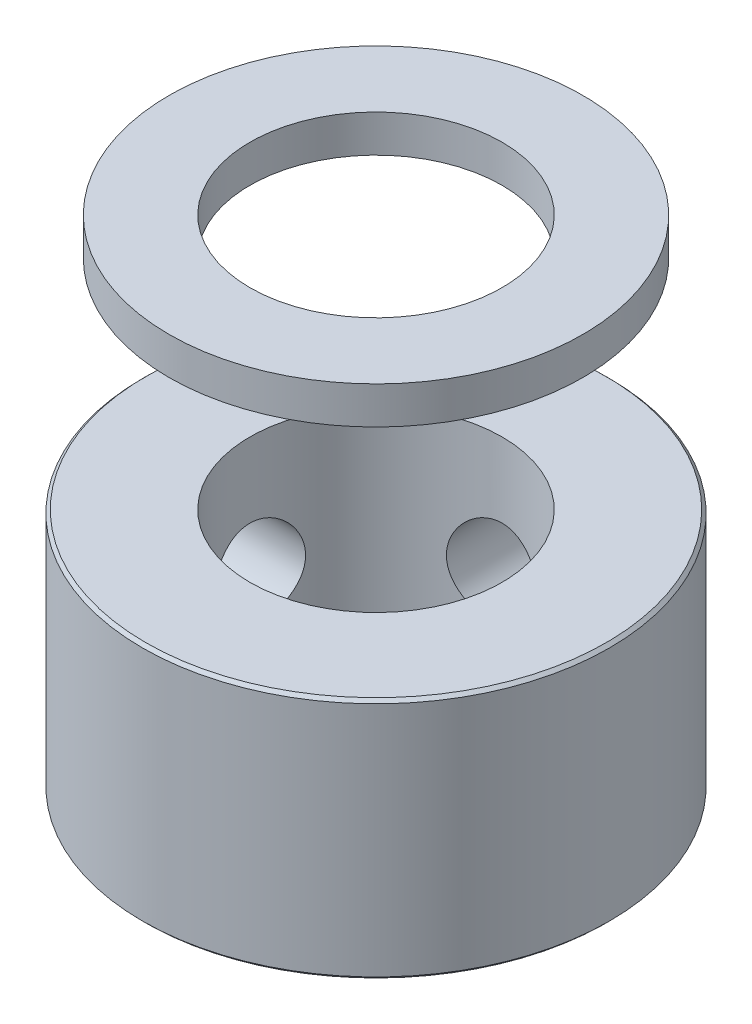
SolidWorks part; units mm, degrees
material "6061 slitina"
ref_plane "Přední rovina" through (0, 0, 0) normal (0, 0, 1) x (1, 0, 0)
ref_plane "Horní rovina" through (0, 0, 0) normal (0, 1, 0) x (1, 0, 0)
ref_plane "Pravá rovina" through (0, 0, 0) normal (1, 0, 0) x (0, 0, -1)
sketch "Skica1" plane through (0, 0, 0) normal (0, 1, 0) x (1, 0, 0)
  circle A0 centre (0, 0) radius 2.5
  arc B0 (-5.7301, 1.0983) -> (-5.3872, 2.2403) centre (-5.6803, 1.7058) ccw
  arc B1 (-5.7301, 1.0983) -> (-5.922, 1.0859) centre (-5.7841, 0.4401) ccw
  arc B2 (-5.922, 1.0859) -> (-6.0197, 1.0387) centre (-5.8743, 0.8624) ccw
  arc B3 (-6.0197, 1.0387) -> (-6.0791, 0.6004) centre (0, 0) ccw
  arc B4 (-6.0791, 0.6004) -> (-5.9974, 0.5289) centre (-5.892, 0.7317) ccw
  arc B5 (-5.9974, 0.5289) -> (-5.8158, 0.466) centre (-5.6927, 1.1148) ccw
  arc B6 (-5.7891, -0.7262) -> (-5.8158, 0.466) centre (-5.9294, -0.133) ccw
  arc B7 (-5.7891, -0.7262) -> (-5.9677, -0.7972) centre (-5.637, -1.3689) ccw
  arc B8 (-5.9677, -0.7972) -> (-6.0461, -0.8723) centre (-5.8532, -0.9951) ccw
  arc B9 (-6.0461, -0.8723) -> (-5.9671, -1.3075) centre (0, 0) ccw
  arc B10 (-5.9671, -1.3075) -> (-5.8673, -1.3503) centre (-5.8297, -1.1248) ccw
  arc B11 (-5.8673, -1.3503) -> (-5.6751, -1.354) centre (-5.7586, -0.6989) ccw
  arc B12 (-5.2813, -2.4796) -> (-5.6751, -1.354) centre (-5.5981, -1.9587) ccw
  arc B13 (-5.2813, -2.4796) -> (-5.4293, -2.6023) centre (-4.9381, -3.0438) ccw
  arc B14 (-5.4293, -2.6023) -> (-5.4806, -2.698) centre (-5.2593, -2.7551) ccw
  arc B15 (-5.4806, -2.698) -> (-5.271, -3.0875) centre (0, 0) ccw
  arc B16 (-5.271, -3.0875) -> (-5.1629, -3.0973) centre (-5.1968, -2.8713) ccw
  arc B17 (-5.1629, -3.0973) -> (-4.979, -3.0415) centre (-5.2608, -2.4442) ccw
  arc B18 (-4.2566, -3.9902) -> (-4.979, -3.0415) centre (-4.7188, -3.5928) ccw
  arc B19 (-4.2566, -3.9902) -> (-4.3594, -4.1527) centre (-3.7559, -4.4208) ccw
  arc B20 (-4.3594, -4.1527) -> (-4.3786, -4.2595) centre (-4.1505, -4.2455) ccw
  arc B21 (-4.3786, -4.2595) -> (-4.059, -4.5652) centre (0, 0) ccw
  arc B22 (-4.059, -4.5652) -> (-3.9531, -4.5412) centre (-4.0552, -4.3366) ccw
  arc B23 (-3.9531, -4.5412) -> (-3.7954, -4.4312) centre (-4.248, -3.9503) ccw
  arc B24 (-2.8152, -5.1103) -> (-3.7954, -4.4312) centre (-3.3776, -4.8751) ccw
  arc B25 (-2.8152, -5.1103) -> (-2.8628, -5.2965) centre (-2.2059, -5.3651) ccw
  arc B26 (-2.8628, -5.2965) -> (-2.8481, -5.4041) centre (-2.6354, -5.3203) ccw
  arc B27 (-2.8481, -5.4041) -> (-2.4496, -5.596) centre (0, 0) ccw
  arc B28 (-2.4496, -5.596) -> (-2.3563, -5.5405) centre (-2.5166, -5.3775) ccw
  arc B29 (-2.3563, -5.5405) -> (-2.2403, -5.3872) centre (-2.8194, -5.0696) ccw
  arc B30 (-1.0983, -5.7301) -> (-2.2403, -5.3872) centre (-1.7058, -5.6803) ccw
  arc B31 (-1.0983, -5.7301) -> (-1.0859, -5.922) centre (-0.4401, -5.7841) ccw
  arc B32 (-1.0859, -5.922) -> (-1.0387, -6.0197) centre (-0.8624, -5.8743) ccw
  arc B33 (-1.0387, -6.0197) -> (-0.6004, -6.0791) centre (0, 0) ccw
  arc B34 (-0.6004, -6.0791) -> (-0.5289, -5.9974) centre (-0.7317, -5.892) ccw
  arc B35 (-0.5289, -5.9974) -> (-0.466, -5.8158) centre (-1.1148, -5.6927) ccw
  arc B36 (0.7262, -5.7891) -> (-0.466, -5.8158) centre (0.133, -5.9294) ccw
  arc B37 (0.7262, -5.7891) -> (0.7972, -5.9677) centre (1.3689, -5.637) ccw
  arc B38 (0.7972, -5.9677) -> (0.8723, -6.0461) centre (0.9951, -5.8532) ccw
  arc B39 (0.8723, -6.0461) -> (1.3075, -5.9671) centre (0, 0) ccw
  arc B40 (1.3075, -5.9671) -> (1.3503, -5.8673) centre (1.1248, -5.8297) ccw
  arc B41 (1.3503, -5.8673) -> (1.354, -5.6751) centre (0.6989, -5.7586) ccw
  arc B42 (2.4796, -5.2813) -> (1.354, -5.6751) centre (1.9587, -5.5981) ccw
  arc B43 (2.4796, -5.2813) -> (2.6023, -5.4293) centre (3.0438, -4.9381) ccw
  arc B44 (2.6023, -5.4293) -> (2.698, -5.4806) centre (2.7551, -5.2593) ccw
  arc B45 (2.698, -5.4806) -> (3.0875, -5.271) centre (0, 0) ccw
  arc B46 (3.0875, -5.271) -> (3.0973, -5.1629) centre (2.8713, -5.1968) ccw
  arc B47 (3.0973, -5.1629) -> (3.0415, -4.979) centre (2.4442, -5.2608) ccw
  arc B48 (3.9902, -4.2566) -> (3.0415, -4.979) centre (3.5928, -4.7188) ccw
  arc B49 (3.9902, -4.2566) -> (4.1527, -4.3594) centre (4.4208, -3.7559) ccw
  arc B50 (4.1527, -4.3594) -> (4.2595, -4.3786) centre (4.2455, -4.1505) ccw
  arc B51 (4.2595, -4.3786) -> (4.5652, -4.059) centre (0, 0) ccw
  arc B52 (4.5652, -4.059) -> (4.5412, -3.9531) centre (4.3366, -4.0552) ccw
  arc B53 (4.5412, -3.9531) -> (4.4312, -3.7954) centre (3.9503, -4.248) ccw
  arc B54 (5.1103, -2.8152) -> (4.4312, -3.7954) centre (4.8751, -3.3776) ccw
  arc B55 (5.1103, -2.8152) -> (5.2965, -2.8628) centre (5.3651, -2.2059) ccw
  arc B56 (5.2965, -2.8628) -> (5.4041, -2.8481) centre (5.3203, -2.6354) ccw
  arc B57 (5.4041, -2.8481) -> (5.596, -2.4496) centre (0, 0) ccw
  arc B58 (5.596, -2.4496) -> (5.5405, -2.3563) centre (5.3775, -2.5166) ccw
  arc B59 (5.5405, -2.3563) -> (5.3872, -2.2403) centre (5.0696, -2.8194) ccw
  arc B60 (5.7301, -1.0983) -> (5.3872, -2.2403) centre (5.6803, -1.7058) ccw
  arc B61 (5.7301, -1.0983) -> (5.922, -1.0859) centre (5.7841, -0.4401) ccw
  arc B62 (5.922, -1.0859) -> (6.0197, -1.0387) centre (5.8743, -0.8624) ccw
  arc B63 (6.0197, -1.0387) -> (6.0791, -0.6004) centre (0, 0) ccw
  arc B64 (6.0791, -0.6004) -> (5.9974, -0.5289) centre (5.892, -0.7317) ccw
  arc B65 (5.9974, -0.5289) -> (5.8158, -0.466) centre (5.6927, -1.1148) ccw
  arc B66 (5.7891, 0.7262) -> (5.8158, -0.466) centre (5.9294, 0.133) ccw
  arc B67 (5.7891, 0.7262) -> (5.9677, 0.7972) centre (5.637, 1.3689) ccw
  arc B68 (5.9677, 0.7972) -> (6.0461, 0.8723) centre (5.8532, 0.9951) ccw
  arc B69 (6.0461, 0.8723) -> (5.9671, 1.3075) centre (0, 0) ccw
  arc B70 (5.9671, 1.3075) -> (5.8673, 1.3503) centre (5.8297, 1.1248) ccw
  arc B71 (5.8673, 1.3503) -> (5.6751, 1.354) centre (5.7586, 0.6989) ccw
  arc B72 (5.2813, 2.4796) -> (5.6751, 1.354) centre (5.5981, 1.9587) ccw
  arc B73 (5.2813, 2.4796) -> (5.4293, 2.6023) centre (4.9381, 3.0438) ccw
  arc B74 (5.4293, 2.6023) -> (5.4806, 2.698) centre (5.2593, 2.7551) ccw
  arc B75 (5.4806, 2.698) -> (5.271, 3.0875) centre (0, 0) ccw
  arc B76 (5.271, 3.0875) -> (5.1629, 3.0973) centre (5.1968, 2.8713) ccw
  arc B77 (5.1629, 3.0973) -> (4.979, 3.0415) centre (5.2608, 2.4442) ccw
  arc B78 (4.2566, 3.9902) -> (4.979, 3.0415) centre (4.7188, 3.5928) ccw
  arc B79 (4.2566, 3.9902) -> (4.3594, 4.1527) centre (3.7559, 4.4208) ccw
  arc B80 (4.3594, 4.1527) -> (4.3786, 4.2595) centre (4.1505, 4.2455) ccw
  arc B81 (4.3786, 4.2595) -> (4.059, 4.5652) centre (0, 0) ccw
  arc B82 (4.059, 4.5652) -> (3.9531, 4.5412) centre (4.0552, 4.3366) ccw
  arc B83 (3.9531, 4.5412) -> (3.7954, 4.4312) centre (4.248, 3.9503) ccw
  arc B84 (2.8152, 5.1103) -> (3.7954, 4.4312) centre (3.3776, 4.8751) ccw
  arc B85 (2.8152, 5.1103) -> (2.8628, 5.2965) centre (2.2059, 5.3651) ccw
  arc B86 (2.8628, 5.2965) -> (2.8481, 5.4041) centre (2.6354, 5.3203) ccw
  arc B87 (2.8481, 5.4041) -> (2.4496, 5.596) centre (0, 0) ccw
  arc B88 (2.4496, 5.596) -> (2.3563, 5.5405) centre (2.5166, 5.3775) ccw
  arc B89 (2.3563, 5.5405) -> (2.2403, 5.3872) centre (2.8194, 5.0696) ccw
  arc B90 (1.0983, 5.7301) -> (2.2403, 5.3872) centre (1.7058, 5.6803) ccw
  arc B91 (1.0983, 5.7301) -> (1.0859, 5.922) centre (0.4401, 5.7841) ccw
  arc B92 (1.0859, 5.922) -> (1.0387, 6.0197) centre (0.8624, 5.8743) ccw
  arc B93 (1.0387, 6.0197) -> (0.6004, 6.0791) centre (0, 0) ccw
  arc B94 (0.6004, 6.0791) -> (0.5289, 5.9974) centre (0.7317, 5.892) ccw
  arc B95 (0.5289, 5.9974) -> (0.466, 5.8158) centre (1.1148, 5.6927) ccw
  arc B96 (-0.7262, 5.7891) -> (0.466, 5.8158) centre (-0.133, 5.9294) ccw
  arc B97 (-0.7262, 5.7891) -> (-0.7972, 5.9677) centre (-1.3689, 5.637) ccw
  arc B98 (-0.7972, 5.9677) -> (-0.8723, 6.0461) centre (-0.9951, 5.8532) ccw
  arc B99 (-0.8723, 6.0461) -> (-1.3075, 5.9671) centre (0, 0) ccw
  arc B100 (-1.3075, 5.9671) -> (-1.3503, 5.8673) centre (-1.1248, 5.8297) ccw
  arc B101 (-1.3503, 5.8673) -> (-1.354, 5.6751) centre (-0.6989, 5.7586) ccw
  arc B102 (-2.4796, 5.2813) -> (-1.354, 5.6751) centre (-1.9587, 5.5981) ccw
  arc B103 (-2.4796, 5.2813) -> (-2.6023, 5.4293) centre (-3.0438, 4.9381) ccw
  arc B104 (-2.6023, 5.4293) -> (-2.698, 5.4806) centre (-2.7551, 5.2593) ccw
  arc B105 (-2.698, 5.4806) -> (-3.0875, 5.271) centre (0, 0) ccw
  arc B106 (-3.0875, 5.271) -> (-3.0973, 5.1629) centre (-2.8713, 5.1968) ccw
  arc B107 (-3.0973, 5.1629) -> (-3.0415, 4.979) centre (-2.4442, 5.2608) ccw
  arc B108 (-3.9902, 4.2566) -> (-3.0415, 4.979) centre (-3.5928, 4.7188) ccw
  arc B109 (-3.9902, 4.2566) -> (-4.1527, 4.3594) centre (-4.4208, 3.7559) ccw
  arc B110 (-4.1527, 4.3594) -> (-4.2595, 4.3786) centre (-4.2455, 4.1505) ccw
  arc B111 (-4.2595, 4.3786) -> (-4.5652, 4.059) centre (0, 0) ccw
  arc B112 (-4.5652, 4.059) -> (-4.5412, 3.9531) centre (-4.3366, 4.0552) ccw
  arc B113 (-4.5412, 3.9531) -> (-4.4312, 3.7954) centre (-3.9503, 4.248) ccw
  arc B114 (-5.1103, 2.8152) -> (-4.4312, 3.7954) centre (-4.8751, 3.3776) ccw
  arc B115 (-5.1103, 2.8152) -> (-5.2965, 2.8628) centre (-5.3651, 2.2059) ccw
  arc B116 (-5.2965, 2.8628) -> (-5.4041, 2.8481) centre (-5.3203, 2.6354) ccw
  arc B117 (-5.4041, 2.8481) -> (-5.596, 2.4496) centre (0, 0) ccw
  arc B118 (-5.596, 2.4496) -> (-5.5405, 2.3563) centre (-5.3775, 2.5166) ccw
  arc B119 (-5.5405, 2.3563) -> (-5.3872, 2.2403) centre (-5.0696, 2.8194) ccw
  dimension "D1" = 5
sketch_block_instance "Blok1-1"
sketch_block "Blok1"
extrude "Přidat vysunutím1" add sketch "Skica1" along normal blind 7 from offset 7.8
sketch "Skica2" plane through (0, 7.8, 0) normal (0, -1, 0) x (1, 0, 0)
  circle A0 centre (0, 0) radius 3.5
  circle A1 centre (0, 0) radius 2.5 construction
  circle A2 centre (0, 0) radius 2.5
  dimension "D1" = 7
extrude "Přidat vysunutím2" add sketch "Skica2" along normal blind 7.8
sketch "Skica3" plane through (0, 14.8, 0) normal (0, 1, 0) x (1, 0, 0)
  circle A0 centre (0, 0) radius 3.5
  circle A1 centre (0, 0) radius 2.5 construction
  circle A2 centre (0, 0) radius 2.5
  dimension "D1" = 7
extrude "Přidat vysunutím3" add sketch "Skica3" along normal blind 1.2
sketch "Skica5" plane through (0, 16, 0) normal (0, 1, 0) x (1, 0, 0)
  circle A0 centre (0, 0) radius 7.5
  circle A3 centre (0, 0) radius 3.5 construction
  circle A4 centre (0, 0) radius 3.5
  dimension "D1" = 15
extrude "Přidat vysunutím4" add sketch "Skica5" against normal up to surface (1.2 mm away) separate body up to face at (0, 14.8, 0)
sketch "Skica6" plane through (0, 0, 0) normal (0, -1, 0) x (1, 0, 0)
  circle A0 centre (0, 0) radius 7.5
  circle A1 centre (0, 0) radius 3.5 construction
  circle A2 centre (0, 0) radius 3.5
  circle A3 centre (0, 0) radius 7.5 construction
extrude "Přidat vysunutím5" add sketch "Skica6" against normal up to surface (7.8 mm away) separate body up to face at (0, 7.8, 0)
chamfer "Zkosení1" distance 0.1 angle 45 2 edges at (0, 14.8, 7.5) (0, 16, 7.5)
chamfer "Zkosení2" distance 0.1 angle 45 2 edges at (0, 0, -2.5) (0, 16, 2.5)
chamfer "Zkosení3" distance 0.1 angle 45 2 edges at (0, 0, -7.5) (0, 7.8, 7.5)
sketch "Sketch7" plane through (0, 0, 0) normal (0, -1, 0) x (1, 0, 0)
  circle A1 centre (0, 0) radius 4.05
  dimension "D1" = 8.1
sketch "Sketch8" plane through (0, 16, 0) normal (0, 1, 0) x (1, 0, 0)
  circle A0 centre (0, 0) radius 6.65
extrude "Cut-Extrude2" cut sketch "Sketch8" against normal blind 5 flip side to cut contours A0
ref_plane "Plane1" through (0, 0, -7.5) normal (0, 0, -1) x (-1, 0, 0)
ref_plane "Plane2" through (-7.5, 0, 0) normal (-1, 0, 0) x (0, 0, 1)
sketch "Sketch19" plane through (0, 0, -7.5) normal (0, 0, -1) x (-1, 0, 0)
  line L0 (0, 0.1) -> (0, 7.7)
  line L1 (7.5, 0.1) -> (-7.5, 0.1) construction
  line L2 (7.5, 7.7) -> (-7.5, 7.7) construction
  circle A0 centre (0, 3.9) radius 1.5
extrude "Cut-Extrude6" cut sketch "Sketch19" against normal blind 5 contours A0
sketch "Sketch20" plane through (-7.5, 0, 0) normal (-1, 0, 0) x (0, 0, 1)
  line L0 (0, 0.1) -> (0, 7.7)
  line L1 (-7.5, 0.1) -> (7.5, 0.1) construction
  line L2 (7.5, 7.7) -> (-7.5, 7.7) construction
  circle A0 centre (0, 3.9) radius 1.5
extrude "Cut-Extrude7" cut sketch "Sketch20" against normal blind 5 contours A0
extrude "Cut-Extrude9" cut sketch "Sketch7" against normal blind 20 contours A1
sketch "Sketch23" plane through (0, 0, 0) normal (0, 1, 0) x (1, 0, 0)
  line L1 (0, 7.34) -> (-6.3566, -3.67)
  line L2 (-6.3566, -3.67) -> (6.3566, -3.67)
  line L3 (6.3566, -3.67) -> (0, 7.34)
  circle A0 centre (0, 0) radius 3.67 construction
sketch "Sketch25" plane through (0, 7.8, 0) normal (0, 1, 0) x (1, 0, 0)
  line L0 (-0.7179, 6.0965) -> (-0.9071, 5.7689)
  line L5 (-5.5084, -3.67) -> (-4.5368, -3.67)
  line L6 (5.926, -2.9242) -> (5.4338, -2.0716)
  line L9 (-5.4363, -2.0759) -> (-5.8989, -2.8773)
  line L23 (-3.4987, -3.67) -> (-2.5208, -3.67)
  line L24 (-4.4422, -0.3541) -> (-4.912, -1.1678)
  line L26 (-1.4992, -3.67) -> (-0.513, -3.67)
  line L27 (2.4958, -3.67) -> (3.5189, -3.67)
  line L28 (4.926, -1.192) -> (4.4459, -0.3606)
  line L29 (4.549, -3.67) -> (5.5306, -3.67)
  line L30 (0.5086, -3.67) -> (1.4742, -3.67)
  line L31 (3.9112, 0.5657) -> (3.4185, 1.419)
  line L32 (1.9163, 4.0209) -> (1.4364, 4.8521)
  line L33 (-1.4233, 4.8748) -> (-1.9185, 4.0171)
  line L34 (2.9152, 2.2908) -> (2.4274, 3.1357)
  line L35 (0.9141, 5.7568) -> (0.4321, 6.5916)
  line L37 (-2.4409, 3.1122) -> (-2.9162, 2.2891)
  line L39 (-0.7179, 6.0965) -> (-0.4321, 6.5916)
  line L40 (-3.4352, 1.3901) -> (-3.9277, 0.5371)
  line L42 (-0.4321, 6.5916) -> (-0.9071, 5.7689) [skipped]
  arc A24 (-0.4321, 6.5916) -> (0.4321, 6.5916) centre (0, 6.94) ccw
  arc A25 (-1.4233, 4.8748) -> (-0.9071, 5.7689) centre (-0.9887, 5.22) ccw
  arc A26 (-2.4409, 3.1122) -> (-1.9185, 4.0171) centre (-2.0176, 3.471) ccw
  arc A27 (0.9141, 5.7568) -> (1.4364, 4.8521) centre (1.0128, 5.2106) ccw
  arc A28 (1.9163, 4.0209) -> (2.4274, 3.1357) centre (1.9844, 3.4701) ccw
  arc A29 (-3.4352, 1.3901) -> (-2.9162, 2.2891) centre (-3.0054, 1.7413) ccw
  arc A30 (-4.4422, -0.3541) -> (-3.9277, 0.5371) centre (-4.0048, -0.0125) ccw
  arc A31 (-5.4363, -2.0759) -> (-4.912, -1.1678) centre (-5.0165, -1.7129) ccw
  arc A32 (-5.5084, -3.67) -> (-5.8989, -2.8773) centre (-6.0049, -3.4221) ccw
  arc A33 (-3.4987, -3.67) -> (-4.5368, -3.67) centre (-4.0177, -3.4735) ccw
  arc A34 (-1.4992, -3.67) -> (-2.5208, -3.67) centre (-2.01, -3.4529) ccw
  arc A35 (0.5086, -3.67) -> (-0.513, -3.67) centre (-0.0022, -3.4529) ccw
  arc A36 (2.4958, -3.67) -> (1.4742, -3.67) centre (1.985, -3.4529) ccw
  arc A37 (4.549, -3.67) -> (3.5189, -3.67) centre (4.0339, -3.4632) ccw
  arc A38 (2.9152, 2.2908) -> (3.4185, 1.419) centre (2.9643, 1.738) ccw
  arc A39 (3.9112, 0.5657) -> (4.4459, -0.3606) centre (4.05, 0.0283) ccw
  arc A40 (4.926, -1.192) -> (5.4338, -2.0716) centre (4.9859, -1.7438) ccw
  arc A41 (5.926, -2.9242) -> (5.5306, -3.67) centre (6.0467, -3.4659) ccw
  point P0 (-1.0017, 5.205)
  point P6 (-2.0034, 3.47)
  point P7 (-3.0051, 1.735)
  point P9 (-4.0068, 0)
  point P10 (-5.0085, -1.735)
  point P11 (5.0085, -1.735)
  point P12 (4.0068, 0)
  point P13 (3.0051, 1.735)
  point P14 (2.0034, 3.47)
  point P15 (1.0017, 5.205)
  point P16 (-4.0068, -3.47)
  point P20 (-2.0034, -3.47)
  point P21 (0, -3.47)
  point P22 (0, 0)
  point P23 (2.0034, -3.47)
  point P24 (4.0068, -3.47)
  point P26 (0, 0)
sketch "Sketch27" plane through (0, 7.8, 0) normal (0, 1, 0) x (1, 0, 0)
  circle A0 centre (0, 0) radius 7.4
extrude "Cut-Extrude12" cut sketch "Sketch27" along normal blind 7 contours A0
